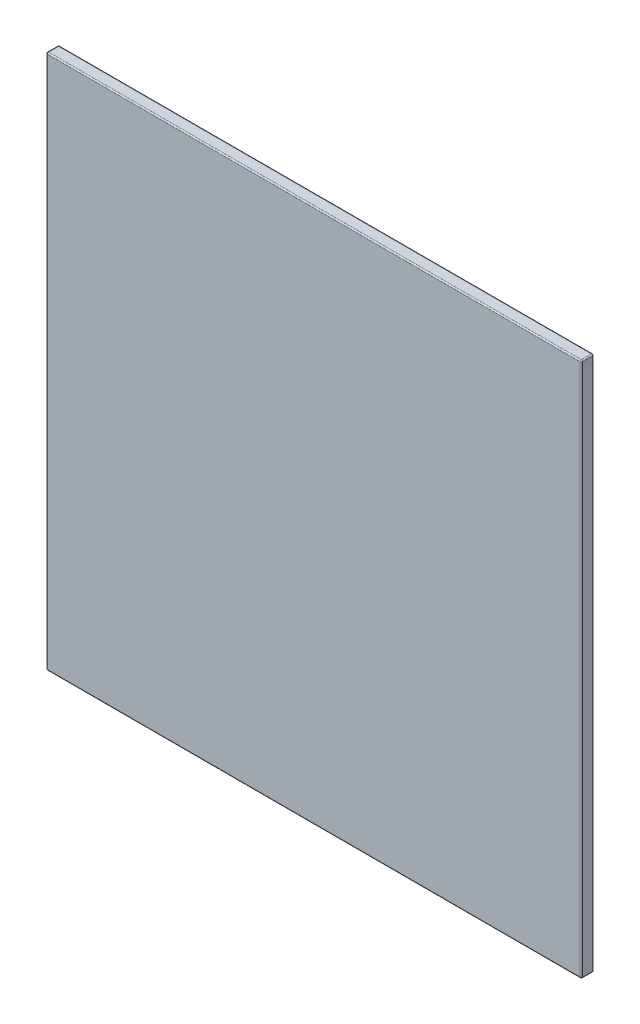
SolidWorks part; units mm, degrees
material "1060 Alloy"
ref_plane "Front Plane" through (0, 0, 0) normal (0, 0, 1) x (1, 0, 0)
ref_plane "Top Plane" through (0, 0, 0) normal (0, 1, 0) x (1, 0, 0)
ref_plane "Right Plane" through (0, 0, 0) normal (1, 0, 0) x (0, 0, -1)
sketch "Sketch1" plane through (0, 0, 0) normal (0, 0, 1) x (1, 0, 0)
  line L1 (-173.2919, 233.3851) -> (126.7081, 233.3851)
  line L2 (-173.2919, 233.3851) -> (-173.2919, -66.6149)
  line L3 (-173.2919, -66.6149) -> (126.7081, -66.6149)
  line L4 (126.7081, 233.3851) -> (126.7081, -66.6149)
  line L5 (-173.2919, 233.3851) -> (126.7081, -66.6149) construction
  line L6 (-173.2919, -66.6149) -> (126.7081, 233.3851) construction
  point P0 (-23.2919, 83.3851)
  dimension "D1" = 300
  dimension "D2" = 300
extrude "Boss-Extrude1" add sketch "Sketch1" along normal blind 7
fillet "Fillet1" radius 0.7 12 edges at (126.7081, 233.3851, 3.5) (126.7081, 83.3851, 0) (126.7081, 83.3851, 7) (126.7081, -66.6149, 3.5) (-23.2919, -66.6149, 0) (-23.2919, -66.6149, 7) (-173.2919, -66.6149, 3.5) (-173.2919, 233.3851, 3.5) (-173.2919, 83.3851, 7) (-173.2919, 83.3851, 0) (-23.2919, 233.3851, 7) (-23.2919, 233.3851, 0)
